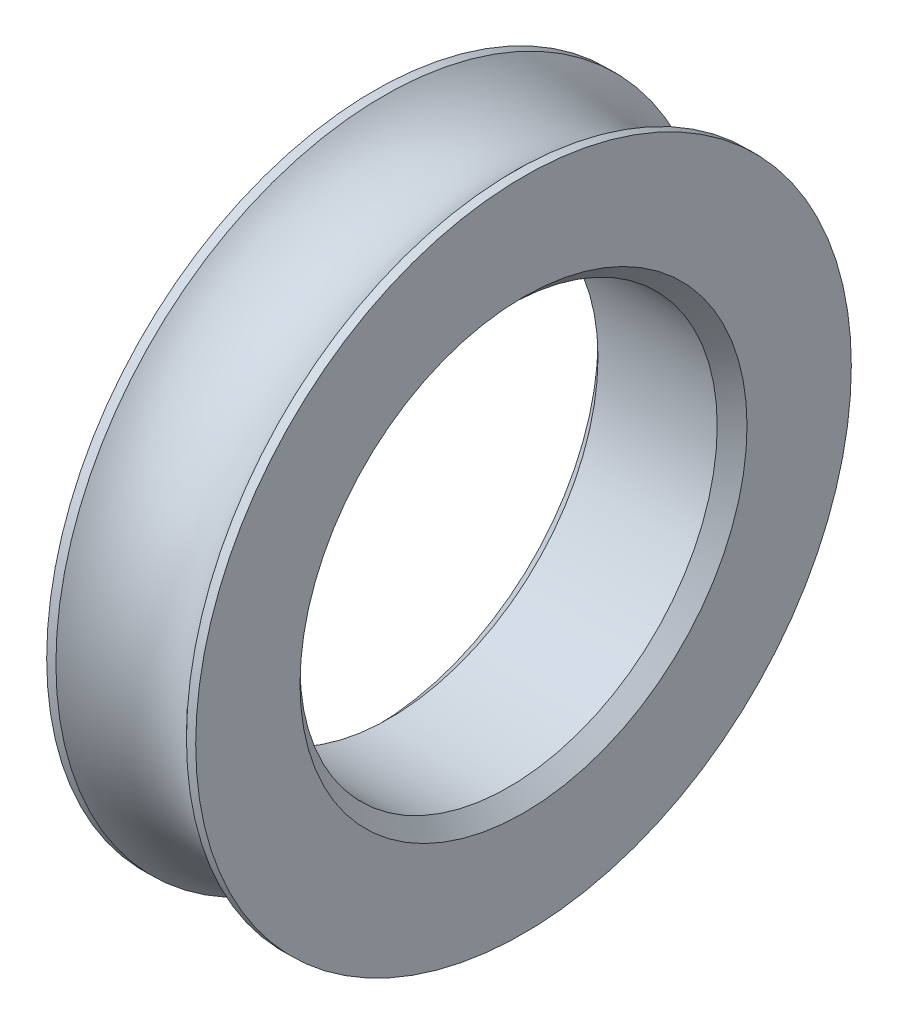
SolidWorks part; units mm, degrees
ref_plane "Front Plane" through (0, 0, 0) normal (0, 0, 1) x (1, 0, 0)
ref_plane "Top Plane" through (0, 0, 0) normal (0, 1, 0) x (1, 0, 0)
ref_plane "Right Plane" through (0, 0, 0) normal (1, 0, 0) x (0, 0, -1)
sketch "Sketch1" plane through (0, 0, 0) normal (0, 0, 1) x (1, 0, 0)
  line L0 (-15.9375, 0) -> (15.9375, 0) construction
  line L1 (0, -21.8982) -> (0, 21.8982) construction
  line L2 (-2.5, 11) -> (-2.1903, 11)
  line L3 (-2.5, 7) -> (2.5, 7)
  line L4 (-2.5, 7) -> (-2.5, 11)
  line L5 (2.5, 11) -> (2.1903, 11)
  line L6 (2.5, 7) -> (2.5, 11)
  line L7 (-2.5, 7) -> (2.5, 11) construction
  line L8 (-2.5, 11) -> (2.5, 7) construction
  arc A0 (-2.1903, 11) -> (2.1903, 11) centre (0, 13.05) ccw
  point P0 (0, 9)
  point P4 (0, 0)
  point P7 (0, 0)
  dimension "D5" = 3
  dimension "D1" = 5
  dimension "D2" = 4
  dimension "D3" = 11
revolve "Revolve1" add sketch "Sketch1" angle 360 about L0
chamfer "Chamfer1" distance 0.5 angle 45 2 edges at (-2.5, 0, 7) (2.5, 0, 7)
